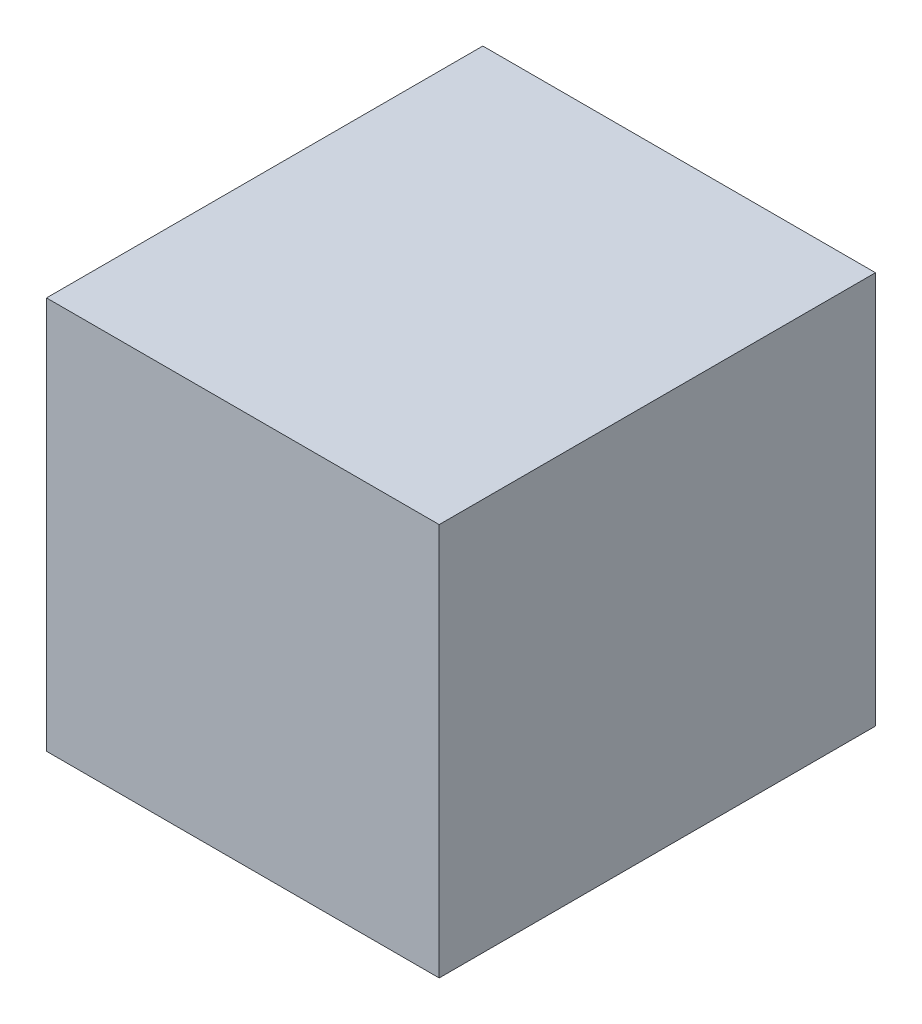
SolidWorks part; units mm, degrees
ref_plane "Płaszczyzna przednia" through (0, 0, 0) normal (0, 0, 1) x (1, 0, 0)
ref_plane "Płaszczyzna górna" through (0, 0, 0) normal (0, 1, 0) x (1, 0, 0)
ref_plane "Płaszczyzna prawa" through (0, 0, 0) normal (1, 0, 0) x (0, 0, -1)
sketch "Szkic1" plane through (0, 0, 0) normal (0, 0, 1) x (1, 0, 0)
  line L1 (21.6, -21.6) -> (-21.6, -21.6)
  line L2 (21.6, -21.6) -> (21.6, 21.6)
  line L3 (21.6, 21.6) -> (-21.6, 21.6)
  line L4 (-21.6, -21.6) -> (-21.6, 21.6)
  line L5 (21.6, -21.6) -> (-21.6, 21.6) construction
  line L6 (21.6, 21.6) -> (-21.6, -21.6) construction
  point P0 (0, 0)
  dimension "D1" = 43.2
  dimension "D2" = 43.2
extrude "Dodanie-wyciągnięcie1" add sketch "Szkic1" along normal blind 48
